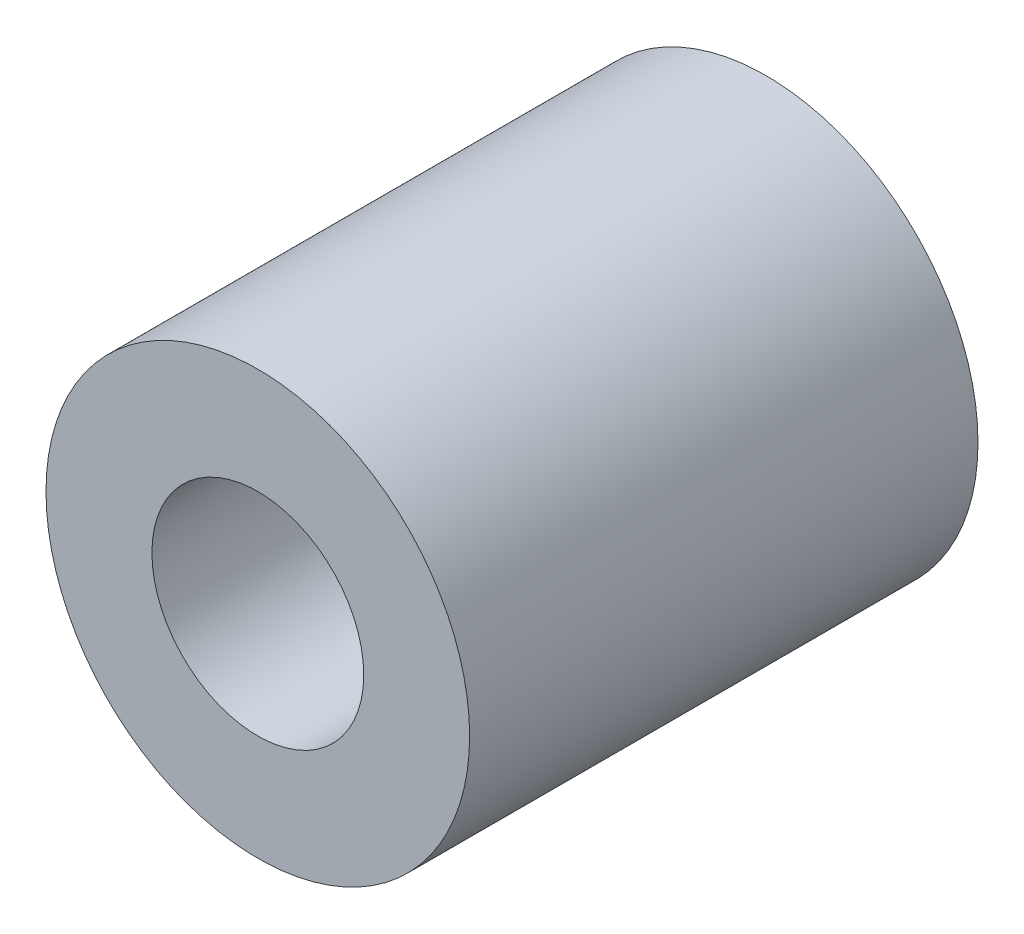
SolidWorks part; units mm, degrees
ref_plane "Plan de face" through (0, 0, 0) normal (0, 0, 1) x (1, 0, 0)
ref_plane "Plan de dessus" through (0, 0, 0) normal (0, 1, 0) x (1, 0, 0)
ref_plane "Plan de droite" through (0, 0, 0) normal (1, 0, 0) x (0, 0, -1)
sketch "Esquisse1" plane through (0, 0, 0) normal (0, 0, 1) x (1, 0, 0)
  circle A0 centre (0, 0) radius 5
  circle A1 centre (0, 0) radius 2.5
extrude "Extrusion1" add sketch "Esquisse1" along normal blind 12
